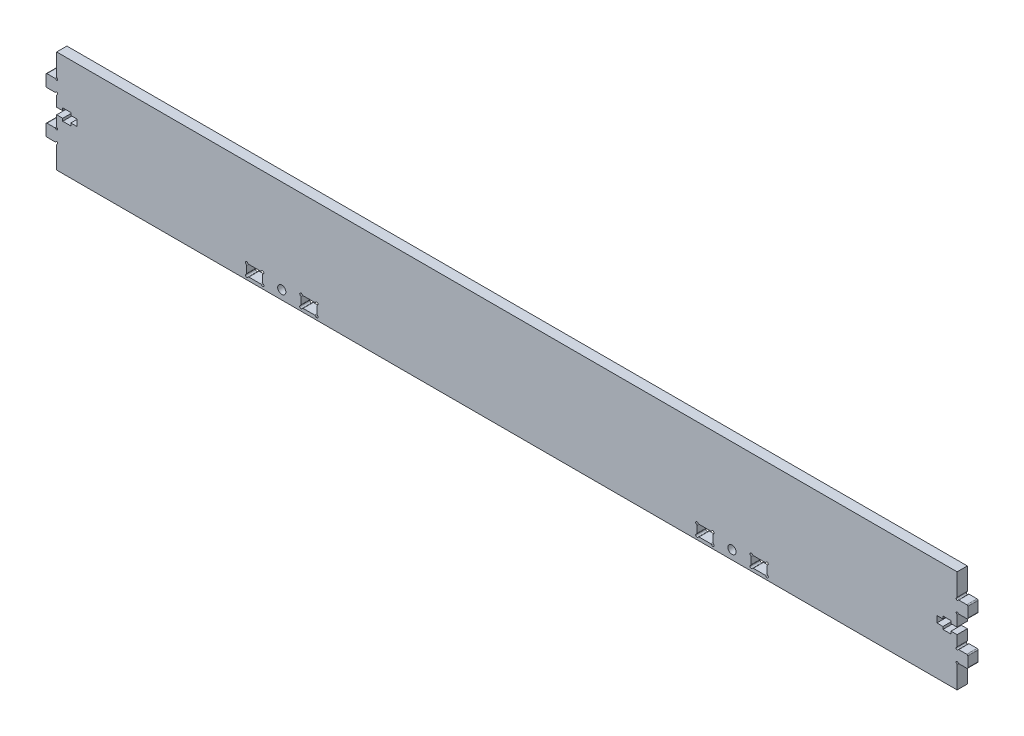
SolidWorks part; units mm, degrees
ref_plane "Alzado" through (0, 0, 0) normal (0, 0, 1) x (1, 0, 0)
ref_plane "Planta" through (0, 0, 0) normal (0, 1, 0) x (1, 0, 0)
ref_plane "Vista lateral" through (0, 0, 0) normal (1, 0, 0) x (0, 0, -1)
sketch "Croquis1" plane through (0, 0, 0) normal (0, 0, 1) x (1, 0, 0)
  line L0 (-176, 0) -> (-196, 0) construction
  line L1 (-175.9989, 20) -> (176.0011, 20)
  line L2 (-175.9989, 20) -> (-175.9989, 11.4487)
  line L3 (-175.9989, -20) -> (176.0011, -20)
  line L4 (-176.6843, -10.7633) -> (-179.7689, -10.7633)
  line L7 (176.0011, 1.2663) -> (176.0011, -1.2663) construction
  line L12 (-175.9989, -11.4487) -> (-175.9989, -20)
  line L27 (-168.0847, 0) -> (168.0869, 0) construction
  line L36 (-175.9989, -18.5) -> (176.0011, -18.5) construction
  line L46 (-175.9989, -14.5) -> (176.0011, -14.5) construction
  line L47 (-180.1646, -10.3676) -> (-180.1646, -6.4105)
  line L48 (-179.7689, -6.0148) -> (-176.6843, -6.0148)
  line L49 (-175.9989, -1.2663) -> (-173.6247, -1.2663)
  line L50 (-173.6247, -1.2663) -> (-173.6247, -2.2753)
  line L51 (-173.6247, -2.2753) -> (-170.459, -2.2753)
  line L52 (-170.459, -2.2753) -> (-170.459, -1.2663)
  line L53 (-170.459, -1.2663) -> (-168.0847, -1.2663)
  line L54 (-168.0847, -1.2663) -> (-168.0847, 1.2663)
  line L55 (-168.0847, 1.2663) -> (-170.459, 1.2663)
  line L56 (-170.459, 1.2663) -> (-170.459, 2.2753)
  line L57 (-170.459, 2.2753) -> (-173.6247, 2.2753)
  line L58 (-173.6247, 2.2753) -> (-173.6247, 1.2663)
  line L59 (-173.6247, 1.2663) -> (-175.9989, 1.2663)
  line L60 (-175.9989, 1.2663) -> (-175.9989, 5.3294)
  line L61 (-176.6843, 6.0148) -> (-179.7689, 6.0148)
  line L62 (-180.1646, 6.4105) -> (-180.1646, 10.3676)
  line L63 (-179.7689, 10.7633) -> (-176.6843, 10.7633)
  line L64 (-175.9989, -1.2663) -> (-175.9989, -5.3294)
  line L65 (176.0011, -11.4487) -> (176.0011, -20)
  line L66 (176.0011, -1.2663) -> (176.0011, -5.3294)
  line L67 (179.7711, 10.7633) -> (176.6865, 10.7633)
  line L68 (180.1668, 6.4105) -> (180.1668, 10.3676)
  line L69 (176.6865, 6.0148) -> (179.7711, 6.0148)
  line L70 (176.0011, 1.2663) -> (176.0011, 5.3294)
  line L71 (173.6269, 1.2663) -> (176.0011, 1.2663)
  line L72 (173.6269, 2.2753) -> (173.6269, 1.2663)
  line L73 (170.4612, 2.2753) -> (173.6269, 2.2753)
  line L74 (170.4612, 1.2663) -> (170.4612, 2.2753)
  line L75 (168.0869, 1.2663) -> (170.4612, 1.2663)
  line L76 (168.0869, -1.2663) -> (168.0869, 1.2663)
  line L77 (170.4612, -1.2663) -> (168.0869, -1.2663)
  line L78 (170.4612, -2.2753) -> (170.4612, -1.2663)
  line L79 (173.6269, -2.2753) -> (170.4612, -2.2753)
  line L80 (173.6269, -1.2663) -> (173.6269, -2.2753)
  line L81 (176.0011, -1.2663) -> (173.6269, -1.2663)
  line L82 (179.7711, -6.0148) -> (176.6865, -6.0148)
  line L83 (180.1668, -10.3676) -> (180.1668, -6.4105)
  line L84 (176.6865, -10.7633) -> (179.7711, -10.7633)
  line L85 (96.3671, -14.35) -> (100.8351, -14.35)
  line L86 (88.0011, -34.8253) -> (88.0011, -20) construction
  line L131 (176.0011, 20) -> (176.0011, 11.4487)
  line L136 (101.7011, -15.2161) -> (101.7011, -17.7839)
  line L138 (-87.9989, -34.8253) -> (-87.9989, -20) construction
  line L139 (100.8351, -18.65) -> (96.3671, -18.65)
  line L140 (95.5011, -17.7839) -> (95.5011, -15.2161)
  line L141 (75.1671, -14.35) -> (79.6351, -14.35)
  line L142 (80.5011, -15.2161) -> (80.5011, -17.7839)
  line L143 (79.6351, -18.65) -> (75.1671, -18.65)
  line L144 (74.3011, -17.7839) -> (74.3011, -15.2161)
  line L145 (-87.9989, -18.5) -> (-87.9989, -14.5) construction
  line L146 (-101.6989, -17.7839) -> (-101.6989, -15.2161)
  line L147 (-74.2989, -15.2161) -> (-74.2989, -17.7839)
  line L148 (-95.4989, -15.2161) -> (-95.4989, -17.7839)
  line L149 (-96.3649, -18.65) -> (-100.8329, -18.65)
  line L150 (-100.8329, -14.35) -> (-96.3649, -14.35)
  line L151 (-79.6329, -14.35) -> (-75.1649, -14.35)
  line L152 (-80.4989, -17.7839) -> (-80.4989, -15.2161)
  line L153 (-75.1649, -18.65) -> (-79.6329, -18.65)
  line L154 (88.0011, -18.5) -> (88.0011, -14.5) construction
  arc A32 (-175.801, -11.106) -> (-175.9989, -11.4487) centre (-175.6032, -11.4487) ccw
  arc A33 (-175.801, -11.106) -> (-176.3416, -10.5654) centre (-175.9989, -10.7633) ccw
  arc A34 (-176.6843, -10.7633) -> (-176.3416, -10.5654) centre (-176.6843, -10.3676) ccw
  arc A35 (-180.1646, -10.3676) -> (-179.7689, -10.7633) centre (-179.7689, -10.3676) ccw
  arc A36 (-179.7689, -6.0148) -> (-180.1646, -6.4105) centre (-179.7689, -6.4105) ccw
  arc A37 (-176.3416, -6.2126) -> (-176.6843, -6.0148) centre (-176.6843, -6.4105) ccw
  arc A38 (-176.3416, -6.2126) -> (-175.801, -5.6721) centre (-175.9989, -6.0148) ccw
  arc A39 (-175.9989, -5.3294) -> (-175.801, -5.6721) centre (-175.6032, -5.3294) ccw
  arc A40 (-175.801, 5.6721) -> (-175.9989, 5.3294) centre (-175.6032, 5.3294) ccw
  arc A41 (-175.801, 5.6721) -> (-176.3416, 6.2126) centre (-175.9989, 6.0148) ccw
  arc A42 (-176.6843, 6.0148) -> (-176.3416, 6.2126) centre (-176.6843, 6.4105) ccw
  arc A43 (-180.1646, 6.4105) -> (-179.7689, 6.0148) centre (-179.7689, 6.4105) ccw
  arc A44 (-179.7689, 10.7633) -> (-180.1646, 10.3676) centre (-179.7689, 10.3676) ccw
  arc A45 (-176.3416, 10.5654) -> (-176.6843, 10.7633) centre (-176.6843, 10.3676) ccw
  arc A46 (-176.3416, 10.5654) -> (-175.801, 11.106) centre (-175.9989, 10.7633) ccw
  arc A47 (-175.9989, 11.4487) -> (-175.801, 11.106) centre (-175.6032, 11.4487) ccw
  arc A48 (176.0011, 11.4487) -> (175.8033, 11.106) centre (175.6054, 11.4487) cw
  arc A49 (176.3438, 10.5654) -> (175.8033, 11.106) centre (176.0011, 10.7633) cw
  arc A50 (176.3438, 10.5654) -> (176.6865, 10.7633) centre (176.6865, 10.3676) cw
  arc A51 (179.7711, 10.7633) -> (180.1668, 10.3676) centre (179.7711, 10.3676) cw
  arc A52 (180.1668, 6.4105) -> (179.7711, 6.0148) centre (179.7711, 6.4105) cw
  arc A53 (176.6865, 6.0148) -> (176.3438, 6.2126) centre (176.6865, 6.4105) cw
  arc A54 (175.8033, 5.6721) -> (176.3438, 6.2126) centre (176.0011, 6.0148) cw
  arc A55 (175.8033, 5.6721) -> (176.0011, 5.3294) centre (175.6054, 5.3294) cw
  arc A56 (176.0011, -5.3294) -> (175.8033, -5.6721) centre (175.6054, -5.3294) cw
  arc A57 (176.3438, -6.2126) -> (175.8033, -5.6721) centre (176.0011, -6.0148) cw
  arc A58 (176.3438, -6.2126) -> (176.6865, -6.0148) centre (176.6865, -6.4105) cw
  arc A59 (179.7711, -6.0148) -> (180.1668, -6.4105) centre (179.7711, -6.4105) cw
  arc A60 (180.1668, -10.3676) -> (179.7711, -10.7633) centre (179.7711, -10.3676) cw
  arc A61 (176.6865, -10.7633) -> (176.3438, -10.5654) centre (176.6865, -10.3676) cw
  arc A62 (175.8033, -11.106) -> (176.3438, -10.5654) centre (176.0011, -10.7633) cw
  arc A63 (175.8033, -11.106) -> (176.0011, -11.4487) centre (175.6054, -11.4487) cw
  arc A96 (95.5011, -15.2161) -> (95.2511, -14.7831) centre (95.0011, -15.2161) ccw
  arc A97 (95.9341, -14.1) -> (95.2511, -14.7831) centre (95.5011, -14.35) ccw
  arc A98 (95.9341, -14.1) -> (96.3671, -14.35) centre (96.3671, -13.85) ccw
  arc A99 (100.8351, -14.35) -> (101.2681, -14.1) centre (100.8351, -13.85) ccw
  arc A100 (101.9511, -14.783) -> (101.2681, -14.1) centre (101.7011, -14.35) ccw
  arc A101 (101.9511, -14.783) -> (101.7011, -15.2161) centre (102.2011, -15.2161) ccw
  arc A102 (101.7011, -17.7839) -> (101.9511, -18.2169) centre (102.2011, -17.7839) ccw
  arc A103 (101.2681, -18.9) -> (101.9511, -18.2169) centre (101.7011, -18.65) ccw
  arc A104 (101.2681, -18.9) -> (100.8351, -18.65) centre (100.8351, -19.15) ccw
  arc A105 (96.3671, -18.65) -> (95.9341, -18.9) centre (96.3671, -19.15) ccw
  arc A106 (95.2511, -18.2169) -> (95.9341, -18.9) centre (95.5011, -18.65) ccw
  arc A107 (95.2511, -18.2169) -> (95.5011, -17.7839) centre (95.0011, -17.7839) ccw
  arc A108 (74.3011, -15.2161) -> (74.0511, -14.7831) centre (73.8011, -15.2161) ccw
  arc A109 (74.7341, -14.1) -> (74.0511, -14.7831) centre (74.3011, -14.35) ccw
  arc A110 (74.7341, -14.1) -> (75.1671, -14.35) centre (75.1671, -13.85) ccw
  arc A111 (79.6351, -14.35) -> (80.0681, -14.1) centre (79.6351, -13.85) ccw
  arc A112 (80.7511, -14.783) -> (80.0681, -14.1) centre (80.5011, -14.35) ccw
  arc A113 (80.7511, -14.783) -> (80.5011, -15.2161) centre (81.0011, -15.2161) ccw
  arc A114 (80.5011, -17.7839) -> (80.7511, -18.2169) centre (81.0011, -17.7839) ccw
  arc A115 (80.0681, -18.9) -> (80.7511, -18.2169) centre (80.5011, -18.65) ccw
  arc A116 (80.0681, -18.9) -> (79.6351, -18.65) centre (79.6351, -19.15) ccw
  arc A117 (75.1671, -18.65) -> (74.7341, -18.9) centre (75.1671, -19.15) ccw
  arc A118 (74.0511, -18.217) -> (74.7341, -18.9) centre (74.3011, -18.65) ccw
  arc A119 (74.0511, -18.217) -> (74.3011, -17.7839) centre (73.8011, -17.7839) ccw
  circle A120 centre (88.0011, -16.5) radius 1.6
  arc A121 (-101.6989, -15.2161) -> (-101.9489, -14.7831) centre (-102.1989, -15.2161) ccw
  arc A122 (-79.6329, -18.65) -> (-80.0659, -18.9) centre (-79.6329, -19.15) ccw
  arc A123 (-74.0489, -14.783) -> (-74.2989, -15.2161) centre (-73.7989, -15.2161) ccw
  arc A124 (-96.3649, -14.35) -> (-95.9319, -14.1) centre (-96.3649, -13.85) ccw
  arc A125 (-95.2489, -14.783) -> (-95.9319, -14.1) centre (-95.4989, -14.35) ccw
  arc A126 (-95.9319, -18.9) -> (-95.2489, -18.2169) centre (-95.4989, -18.65) ccw
  arc A127 (-80.7489, -18.2169) -> (-80.4989, -17.7839) centre (-80.9989, -17.7839) ccw
  circle A128 centre (-87.9989, -16.5) radius 1.6
  arc A129 (-74.2989, -17.7839) -> (-74.0489, -18.2169) centre (-73.7989, -17.7839) ccw
  arc A130 (-101.2659, -14.1) -> (-101.9489, -14.7831) centre (-101.6989, -14.35) ccw
  arc A131 (-80.0659, -14.1) -> (-79.6329, -14.35) centre (-79.6329, -13.85) ccw
  arc A132 (-95.2489, -14.783) -> (-95.4989, -15.2161) centre (-94.9989, -15.2161) ccw
  arc A133 (-80.0659, -14.1) -> (-80.7489, -14.7831) centre (-80.4989, -14.35) ccw
  arc A134 (-101.9489, -18.217) -> (-101.6989, -17.7839) centre (-102.1989, -17.7839) ccw
  arc A135 (-101.2659, -14.1) -> (-100.8329, -14.35) centre (-100.8329, -13.85) ccw
  arc A136 (-80.7489, -18.2169) -> (-80.0659, -18.9) centre (-80.4989, -18.65) ccw
  arc A137 (-95.9319, -18.9) -> (-96.3649, -18.65) centre (-96.3649, -19.15) ccw
  arc A138 (-80.4989, -15.2161) -> (-80.7489, -14.7831) centre (-80.9989, -15.2161) ccw
  arc A139 (-100.8329, -18.65) -> (-101.2659, -18.9) centre (-100.8329, -19.15) ccw
  arc A140 (-75.1649, -14.35) -> (-74.7319, -14.1) centre (-75.1649, -13.85) ccw
  arc A141 (-74.0489, -14.783) -> (-74.7319, -14.1) centre (-74.2989, -14.35) ccw
  arc A142 (-74.7319, -18.9) -> (-74.0489, -18.2169) centre (-74.2989, -18.65) ccw
  arc A143 (-74.7319, -18.9) -> (-75.1649, -18.65) centre (-75.1649, -19.15) ccw
  arc A144 (-95.4989, -17.7839) -> (-95.2489, -18.2169) centre (-94.9989, -17.7839) ccw
  arc A145 (-101.9489, -18.217) -> (-101.2659, -18.9) centre (-101.6989, -18.65) ccw
  circle A146 centre (-87.9989, -16.5) radius 2.8 construction
  circle A147 centre (88.0011, -16.5) radius 2.8 construction
  point P0 (0, 0)
  dimension "D3" = 4
  dimension "D1" = 40
  dimension "D2" = 1.5
extrude "Saliente-Extruir1" add sketch "Croquis1" along normal blind 4
